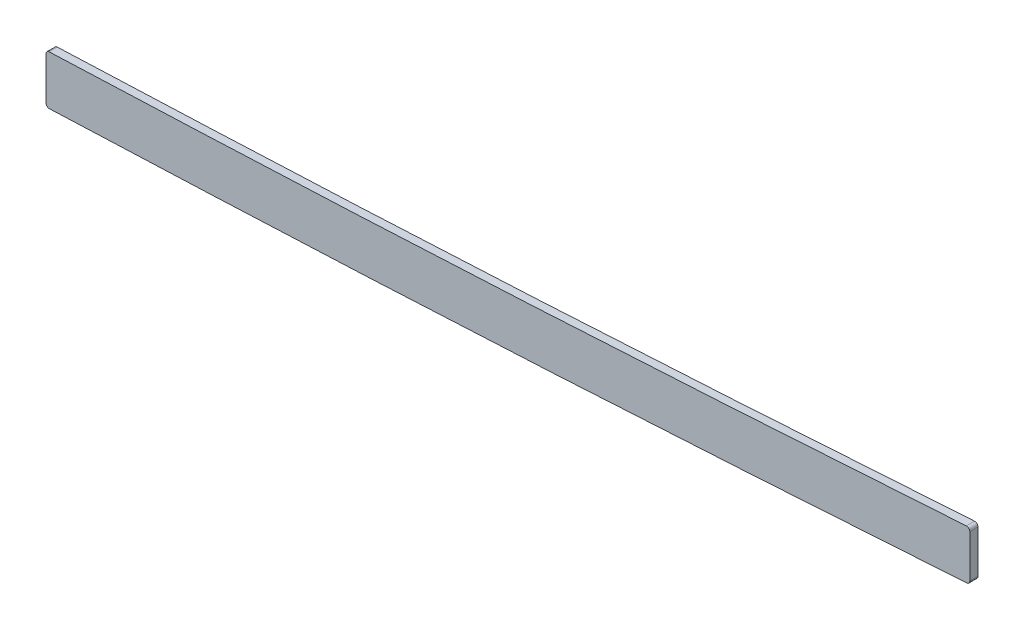
SolidWorks part; units mm, degrees
material "Plywood"
ref_plane "Front Plane" through (0, 0, 0) normal (0, 0, 1) x (1, 0, 0)
ref_plane "Top Plane" through (0, 0, 0) normal (0, 1, 0) x (1, 0, 0)
ref_plane "Right Plane" through (0, 0, 0) normal (1, 0, 0) x (0, 0, -1)
sketch "Sketch1" plane through (0, 0, 0) normal (0, 0, 1) x (1, 0, 0)
  line L0 (1046.2855, 53.4707) -> (499.61, 53.4707) construction
  line L1 (55, 0) -> (-55, 0) construction
  line L2 (1046.2855, -53.4707) -> (499.61, -53.4707)
  line L3 (1046.2855, -34.4207) -> (499.61, -34.4207)
  line L4 (99.06, -18.1493) -> (99.06, -37.7415)
  line L5 (2669.54, 9.5231) -> (2669.54, -9.569)
  line L6 (2311.4, -9.2457) -> (2311.4, -28.3104)
  spline S0 degree 5 poles (2699.7923, 7.5245) (2639.6368, 11.6572) (2579.4813, 15.4358) (2518.4981, 19.1485) (2436.3555, 23.2524) (2354.213, 26.6315) (2332.5703, 27.481) (2156.2686, 34.3778) (1979.9669, 41.6286) (1824.1143, 52.7713) (1636.9286, 53.5796) (1449.7429, 53.454) (1418.0067, 53.4707) (1324.8993, 53.4707) (1231.7919, 53.4707) (1170.4413, 53.4707) (1108.7841, 53.4707) (1047.1269, 53.4707) (1046.8464, 53.4707) (1046.5659, 53.4707) (1046.2855, 53.4707) knots 100.654805 100.654805 100.654805 100.654805 100.654805 100.654805 130.927897 130.927897 130.927897 141.337055 141.337055 141.337055 218.101815 218.101815 218.101815 233.772059 233.772059 233.772059 264.077723 264.077723 264.077723 264.216209 264.216209 264.216209 264.216209 264.216209 264.216209 weights 1 1 1 1 1 1 1 1 1 1 1 1 1 1 1 1 1 1 1 1 1 construction
  spline S1 degree 5 poles (499.61, 53.4707) (492.1368, 53.4707) (484.7543, 53.4707) (477.443, 53.4707) (448.5166, 53.4707) (419.5901, 53.4707) (398.3681, 53.4707) (355.6475, 53.4707) (312.927, 53.4707) (289.2351, 53.4703) (265.365, 53.4707) (241.4948, 53.4707) (241.4716, 53.4707) (241.4484, 53.4707) (241.4251, 53.4707) knots 19.90683 19.90683 19.90683 19.90683 19.90683 19.90683 23.637897 23.637897 23.637897 34.276546 34.276546 34.276546 46.401341 46.401341 46.401341 46.413154 46.413154 46.413154 46.413154 46.413154 46.413154 weights 1 1 1 1 1 1 1 1 1 1 1 1 1 1 1 construction
  spline S2 degree 5 poles (241.4251, 53.4707) (224.2869, 53.4707) (207.1495, 53.4673) (190.2039, 52.6866) (151.6561, 49.0319) (113.1083, 41.5037) (91.9499, 36.3426) (71.313, 30.9696) (50.6762, 24.7565) knots 0 0 0 0 0 0 8.713816 8.713816 8.713816 19.90683 19.90683 19.90683 19.90683 19.90683 19.90683 weights 1 1 1 1 1 1 1 1 1 construction
  spline S3 degree 5 poles (241.4251, -53.4707) (224.2869, -53.4707) (207.1495, -53.4673) (190.2039, -52.6866) (151.6561, -49.0319) (113.1083, -41.5037) (91.9499, -36.3426) (71.313, -30.9696) (50.6762, -24.7565) knots 0 0 0 0 0 0 8.713816 8.713816 8.713816 19.90683 19.90683 19.90683 19.90683 19.90683 19.90683 weights 1 1 1 1 1 1 1 1 1
  spline S4 degree 5 poles (499.61, -53.4707) (492.1368, -53.4707) (484.7543, -53.4707) (477.443, -53.4707) (448.5166, -53.4707) (419.5901, -53.4707) (398.3681, -53.4707) (355.6475, -53.4707) (312.927, -53.4707) (289.2351, -53.4703) (265.365, -53.4707) (241.4948, -53.4707) (241.4716, -53.4707) (241.4484, -53.4707) (241.4251, -53.4707) knots 19.90683 19.90683 19.90683 19.90683 19.90683 19.90683 23.637897 23.637897 23.637897 34.276546 34.276546 34.276546 46.401341 46.401341 46.401341 46.413154 46.413154 46.413154 46.413154 46.413154 46.413154 weights 1 1 1 1 1 1 1 1 1 1 1 1 1 1 1
  spline S5 degree 5 poles (2699.7923, -7.5245) (2639.6368, -11.6572) (2579.4813, -15.4358) (2518.4981, -19.1485) (2436.3555, -23.2524) (2354.213, -26.6315) (2332.5703, -27.481) (2156.2686, -34.3778) (1979.9669, -41.6286) (1824.1143, -52.7713) (1636.9286, -53.5796) (1449.7429, -53.454) (1418.0067, -53.4707) (1324.8993, -53.4707) (1231.7919, -53.4707) (1170.4413, -53.4707) (1108.7841, -53.4707) (1047.1269, -53.4707) (1046.8464, -53.4707) (1046.5659, -53.4707) (1046.2855, -53.4707) knots 100.654805 100.654805 100.654805 100.654805 100.654805 100.654805 130.927897 130.927897 130.927897 141.337055 141.337055 141.337055 218.101815 218.101815 218.101815 233.772059 233.772059 233.772059 264.077723 264.077723 264.077723 264.216209 264.216209 264.216209 264.216209 264.216209 264.216209 weights 1 1 1 1 1 1 1 1 1 1 1 1 1 1 1 1 1 1 1 1 1
  spline S6 degree 1 poles (2698.4867, 11.4807) (1046.2855, -34.4207) knots 0 0 1 1 construction
  spline S7 degree 1 poles (499.61, -34.4207) (241.4252, -34.4207) knots 0 0 1 1 construction
  spline S8 degree 1 poles (241.4252, -34.4207) (56.168, -6.5153) knots 0 0 1 1 construction
  spline S9 degree 3 poles (2698.4867, 11.4807) (2691.2474, 10.9833) (2679.1952, 10.1655) (2662.2765, 9.0388) (2635.6663, 7.2925) (2596.8577, 4.8261) (2545.7297, 1.7583) (2494.4053, -1.0986) (2451.533, -3.2666) (2417.1983, -4.8671) (2391.4571, -6.0036) (2365.6347, -7.0869) (2341.0156, -8.0785) (2320.7508, -8.8784) (2303.4475, -9.5581) (2284.7601, -10.2922) (2261.7633, -11.201) (2227.2853, -12.5838) (2184.1756, -14.3661) (2132.4291, -16.6074) (2063.4255, -19.7089) (1977.1749, -23.7005) (1873.7325, -28.1494) (1770.3746, -31.6575) (1667.0857, -33.7931) (1581.0111, -34.3832) (1512.074, -34.4278) (1443.0615, -34.4095) (1356.8009, -34.4244) (1218.7946, -34.4185) (1115.289, -34.4207) (1046.2855, -34.4207) knots 100.654805 100.654805 100.654805 100.654805 102.842388 104.300777 105.766098 110.877392 115.988686 121.09998 126.211274 128.766921 131.322568 133.878215 136.433862 138.55769 139.835514 141.545156 144.100803 146.656449 151.767743 156.879037 161.990331 172.212919 182.435507 192.658094 202.880682 213.10327 218.214564 223.325858 233.548445 243.771033 264.216209 264.216209 264.216209 264.216209
  spline S10 degree 3 poles (499.61, -34.4207) (488.6147, -34.4207) (472.2364, -34.4207) (449.9402, -34.4207) (427.7713, -34.4207) (405.8747, -34.4207) (384.5849, -34.4207) (368.9002, -34.4207) (353.3766, -34.4207) (332.6085, -34.4207) (306.2878, -34.4206) (274.0235, -34.4205) (252.271, -34.4207) (241.4252, -34.4207) knots 19.90683 19.90683 19.90683 19.90683 23.22012 24.876765 26.533411 29.846701 31.503346 33.159992 34.816637 36.473282 39.786573 43.099863 46.413154 46.413154 46.413154 46.413154
  spline S11 degree 3 poles (241.4252, -34.4207) (239.3949, -34.4207) (235.3223, -34.4205) (227.2744, -34.3987) (217.3194, -34.2975) (205.5307, -33.9764) (189.9633, -33.2126) (170.697, -31.5435) (147.5333, -28.3144) (125.4828, -24.2021) (107.4399, -20.1965) (92.2061, -16.4882) (75.9505, -12.2555) (63.6202, -8.7589) (56.168, -6.5153) knots 0 0 0 0 0.622088 1.244177 2.488354 3.732531 4.976707 7.465061 9.953415 12.441768 14.558235 15.802412 17.418476 19.90683 19.90683 19.90683 19.90683
  point P2 (0, 0)
  dimension "D1" = 50.6762
  dimension "D3" = 99.06
  dimension "D4" = 2669.54
  dimension "D5" = 2311.4
  dimension "D2" = 19.05
extrude "Boss-Extrude1" add sketch "Sketch1" along normal mid plane 3.175 contours L5 S9 L6 S5
fillet "Fillet1" radius 1.27 4 edges at (2669.54, 9.5231, 0) (2311.4, -9.2457, 0)
